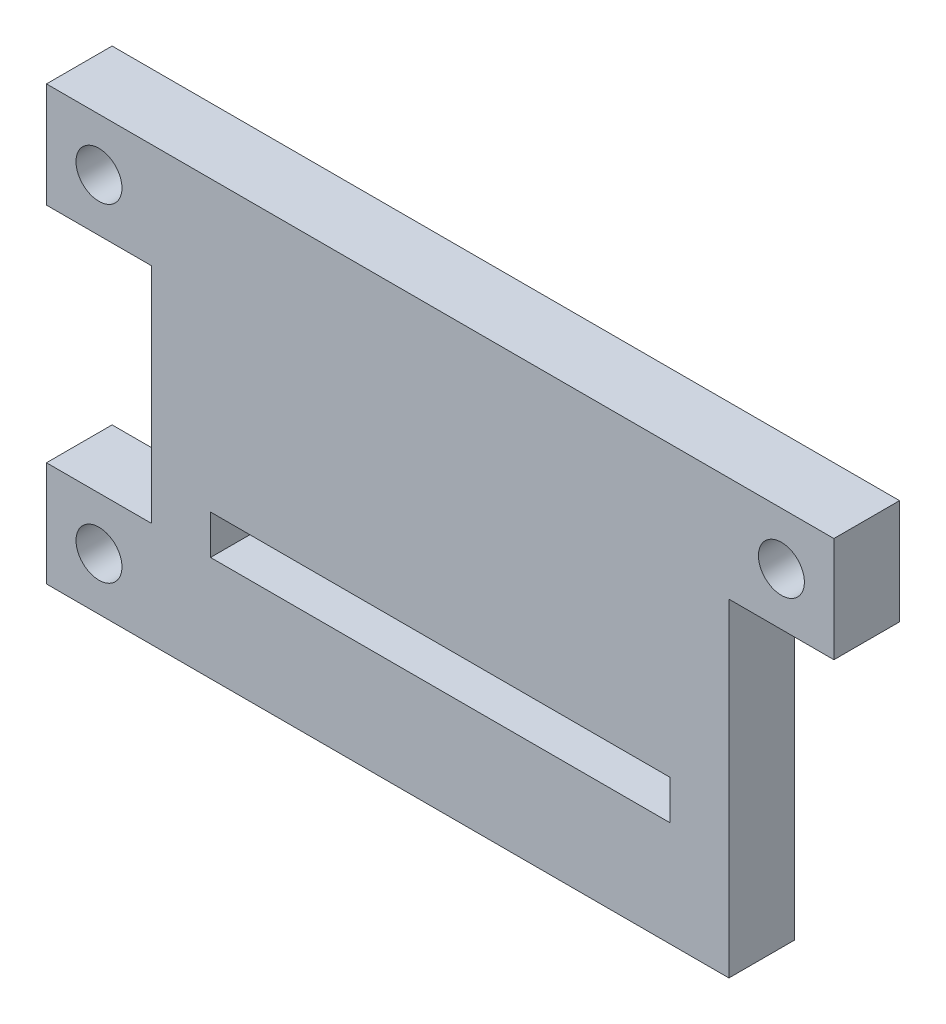
SolidWorks part; units mm, degrees
ref_plane "前基準面" through (0, 0, 0) normal (0, 0, 1) x (1, 0, 0)
ref_plane "上基準面" through (0, 0, 0) normal (0, 1, 0) x (1, 0, 0)
ref_plane "右基準面" through (0, 0, 0) normal (1, 0, 0) x (0, 0, -1)
sketch "草圖1" plane through (0, 0, 0) normal (0, 0, 1) x (1, 0, 0)
  line L1 (-22, 16.5) -> (22, 16.5)
  line L2 (-22, 16.5) -> (-22, -16.5)
  line L3 (-22, -16.5) -> (22, -16.5)
  line L4 (22, 16.5) -> (22, -16.5)
  line L5 (-22, 16.5) -> (22, -16.5) construction
  line L6 (-22, -16.5) -> (22, 16.5) construction
  line L7 (-30, 8.5) -> (-22, 8.5)
  line L8 (-30, 8.5) -> (-30, 16.5)
  line L9 (-30, 16.5) -> (-22, 16.5)
  line L10 (-22, 8.5) -> (-22, 16.5)
  line L11 (-30, 8.5) -> (-22, 16.5) construction
  line L12 (-30, 16.5) -> (-22, 8.5) construction
  line L13 (-30, -8.5) -> (-22, -8.5)
  line L14 (-30, -8.5) -> (-30, -16.5)
  line L15 (-30, -16.5) -> (-22, -16.5)
  line L16 (-22, -8.5) -> (-22, -16.5)
  line L17 (-30, -8.5) -> (-22, -16.5) construction
  line L18 (-30, -16.5) -> (-22, -8.5) construction
  line L19 (30, 8.5) -> (22, 8.5)
  line L20 (30, 8.5) -> (30, 16.5)
  line L21 (30, 16.5) -> (22, 16.5)
  line L22 (22, 8.5) -> (22, 16.5)
  line L23 (30, 8.5) -> (22, 16.5) construction
  line L24 (30, 16.5) -> (22, 8.5) construction
  line L25 (30, -8.5) -> (22, -8.5)
  line L26 (30, -8.5) -> (30, -16.5)
  line L27 (30, -16.5) -> (22, -16.5)
  line L28 (22, -8.5) -> (22, -16.5)
  line L29 (30, -8.5) -> (22, -16.5) construction
  line L30 (30, -16.5) -> (22, -8.5) construction
  circle A0 centre (-26, 12.5) radius 1.75
  circle A1 centre (26, 12.5) radius 1.75
  circle A2 centre (26, -12.5) radius 1.75
  circle A3 centre (-26, -12.5) radius 1.75
  point P0 (0, 0)
  point P6 (-26, 12.5)
  point P7 (-26, -12.5)
  point P11 (26, 12.5)
  point P15 (26, -12.5)
  dimension "D4" = 3.5
  dimension "D1" = 8
  dimension "D2" = 44
  dimension "D3" = 33
extrude "填料-伸長1" add sketch "草圖1" along normal blind 5 contours L9 L8 L7 L2 | L20 L21 L4 L19 | L27 L26 L25 L4 | L14 L15 L2 L13 | L4 L1 L2 L3
sketch "草圖2" plane through (0, 0, 5) normal (0, 0, 1) x (1, 0, 0)
  line L0 (0, -2.75) -> (0, 2.75) construction
  line L1 (-17.5, -5.5) -> (17.5, -5.5)
  line L2 (-17.5, -5.5) -> (-17.5, -8.5)
  line L3 (-17.5, -8.5) -> (17.5, -8.5)
  line L4 (17.5, -5.5) -> (17.5, -8.5)
  line L5 (-17.5, -5.5) -> (17.5, -8.5) construction
  line L6 (-17.5, -8.5) -> (17.5, -5.5) construction
  line L7 (30, -8.5) -> (22, -8.5) construction
  point P0 (0, -7)
  dimension "D1" = 3
  dimension "D2" = 35
extrude "除料-伸長1" cut sketch "草圖2" against normal up to next
sketch "草圖3" plane through (0, 0, 0) normal (0, 0, 1) x (1, 0, 0)
  line L1 (22, -16.5) -> (30, -16.5)
  line L2 (22, -16.5) -> (22, -8.5)
  line L3 (22, -8.5) -> (30, -8.5)
  line L4 (30, -16.5) -> (30, -8.5)
  line L5 (22, -16.5) -> (30, -8.5) construction
  line L6 (22, -8.5) -> (30, -16.5) construction
  point P0 (26, -12.5)
extrude "除料-伸長3" cut sketch "草圖3" along normal through all
